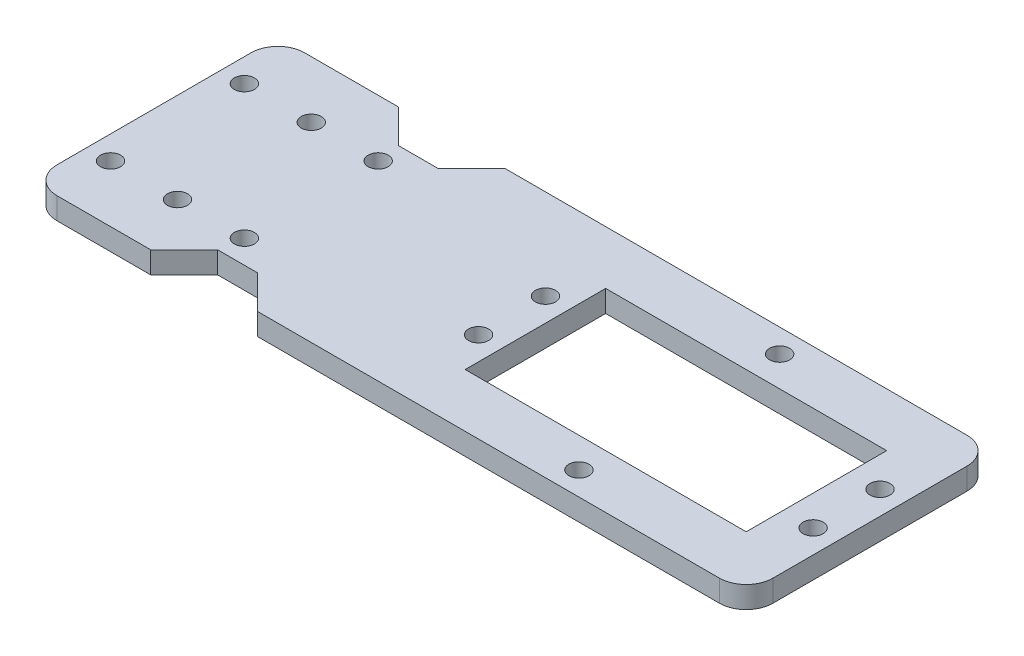
SolidWorks part; units mm, degrees
ref_plane "Front Plane" through (0, 0, 0) normal (0, 0, 1) x (1, 0, 0)
ref_plane "Top Plane" through (0, 0, 0) normal (0, 1, 0) x (1, 0, 0)
ref_plane "Right Plane" through (0, 0, 0) normal (1, 0, 0) x (0, 0, -1)
sketch "Sketch1" plane through (0, 0, 0) normal (0, 1, 0) x (1, 0, 0)
  line L0 (-35.5, 18.5) -> (-35.5, -18.5) construction
  line L1 (-49.5, 18.5) -> (-35.5, 18.5)
  line L2 (-53.5, 14.5) -> (-53.5, -14.5)
  line L3 (-49.5, -18.5) -> (-35.5, -18.5)
  line L4 (53.5, 14.5) -> (53.5, -14.5)
  line L5 (-53.5, 18.5) -> (53.5, -18.5) construction
  line L6 (-19.5, -18.5) -> (-24.5, -13.5)
  line L7 (-24.5, -13.5) -> (-30.5, -13.5)
  line L8 (-30.5, -13.5) -> (-35.5, -18.5)
  line L9 (-35.5, 18.5) -> (-30.5, 13.5)
  line L10 (-30.5, 13.5) -> (-24.5, 13.5)
  line L11 (-24.5, 13.5) -> (-19.5, 18.5)
  line L12 (-19.5, -18.5) -> (49.5, -18.5)
  line L13 (-19.5, 18.5) -> (49.5, 18.5)
  line L14 (45.5, -10.5) -> (45.5, 10.5)
  line L15 (45.5, 10.5) -> (3.5, 10.5)
  line L16 (3.5, 10.5) -> (3.5, -10.5)
  line L17 (3.5, -10.5) -> (45.5, -10.5)
  arc A0 (-49.5, 18.5) -> (-53.5, 14.5) centre (-49.5, 14.5) ccw
  arc A1 (-53.5, -14.5) -> (-49.5, -18.5) centre (-49.5, -14.5) ccw
  arc A2 (49.5, -18.5) -> (53.5, -14.5) centre (49.5, -14.5) ccw
  arc A3 (49.5, 18.5) -> (53.5, 14.5) centre (49.5, 14.5) cw
  circle A19 centre (25, -15) radius 1.5025
  circle A26 centre (-40, -10) radius 1.5025
  circle A28 centre (-30, -10) radius 1.5025
  circle A54 centre (0, -5) radius 1.5025
  circle A64 centre (50, -5) radius 1.5025
  circle A94 centre (0, 5) radius 1.5025
  circle A104 centre (50, 5) radius 1.5025
  circle A106 centre (-40, 10) radius 1.5025
  circle A108 centre (-30, 10) radius 1.5025
  circle A139 centre (25, 15) radius 1.5025
  circle A145 centre (-50, -10) radius 1.5025
  circle A149 centre (-50, 10) radius 1.5025
  point P23 (53.5, 18.5)
  dimension "D8" = 4
  dimension "D11" = 13.5
  dimension "D16" = 3.5
  dimension "D9" = 3.005
  dimension "D10" = 3.005
  dimension "D17" = 8.5
  dimension "D18" = 8.5
  dimension "D19" = 3.5
  dimension "D21" = 4.5
  dimension "D23" = 28.5
  dimension "D24" = 28.5
  dimension "D25" = 3.5
  dimension "D26" = 3.5
  dimension "D27" = 42
  dimension "D28" = 13.5
  dimension "D29" = 8
  dimension "D30" = 13.5
  dimension "D31" = 20
  dimension "D32" = 10
  dimension "D33" = 10
  dimension "D34" = 10
  dimension "D35" = 4.5
  dimension "D36" = 10
  dimension "D37" = 3.5
  dimension "D1" = 107
  dimension "D2" = 37
  dimension "D3" = 18
  dimension "D4" = 16
  dimension "D5" = 6
  dimension "D6" = 16
  dimension "D7" = 27
  dimension "D14" = 8.5
  dimension "D15" = 8.5
  dimension "D12" = 13.5
  dimension "D13" = 20
  dimension "D20" = 21
  dimension "D22" = 3.5
extrude "Boss-Extrude1" add sketch "Sketch1" along normal blind 3.25
